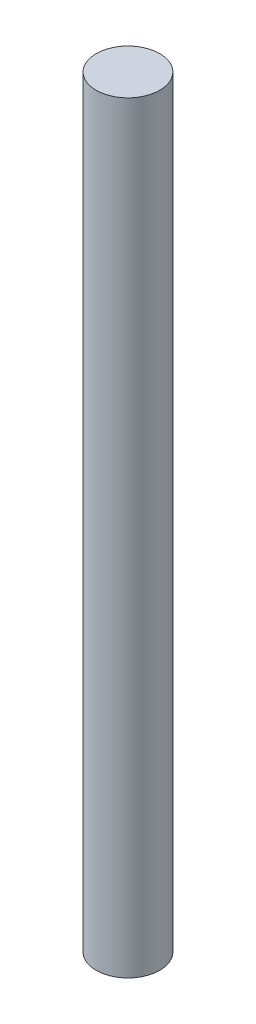
SolidWorks part; units mm, degrees
material "Plain Carbon Steel"
ref_plane "Front Plane" through (0, 0, 0) normal (0, 0, 1) x (1, 0, 0)
ref_plane "Top Plane" through (0, 0, 0) normal (0, 1, 0) x (1, 0, 0)
ref_plane "Right Plane" through (0, 0, 0) normal (1, 0, 0) x (0, 0, -1)
sketch "Sketch1" plane through (0, 0, 0) normal (0, 1, 0) x (1, 0, 0)
  circle A0 centre (0, 0) radius 5
  dimension "D1" = 10
extrude "Boss-Extrude1" add sketch "Sketch1" along normal blind 120
